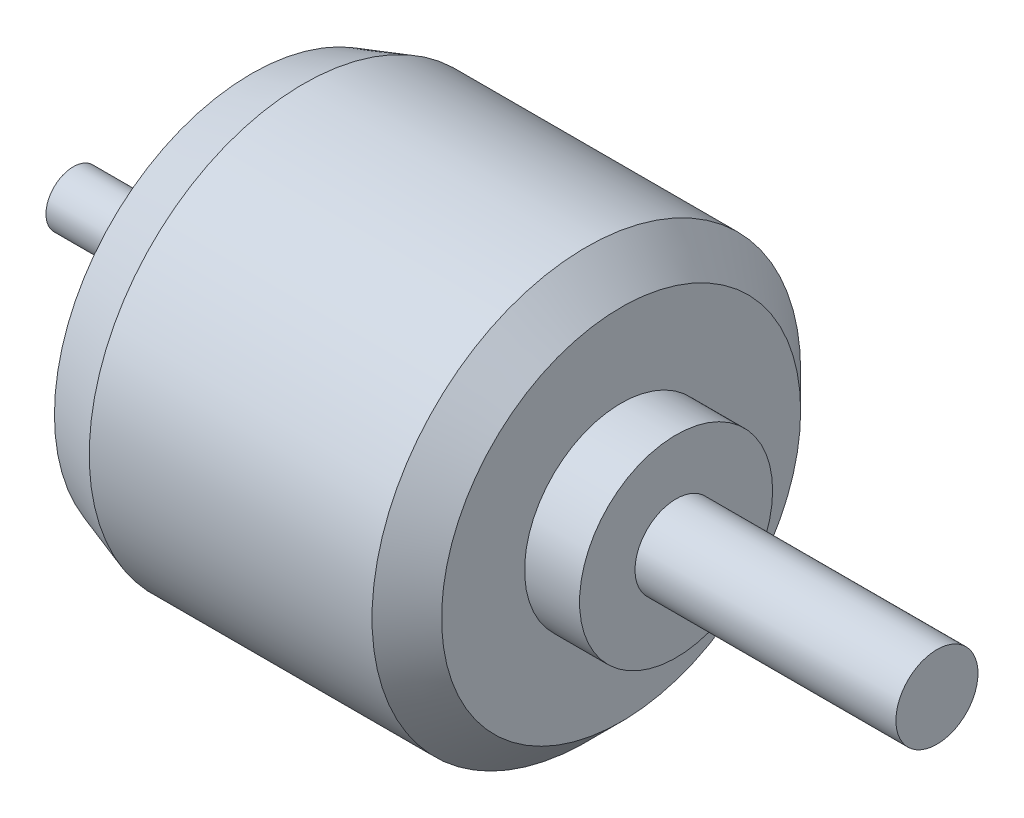
SolidWorks part; units mm, degrees
ref_plane "Front Plane" through (0, 0, 0) normal (0, 0, 1) x (1, 0, 0)
ref_plane "Top Plane" through (0, 0, 0) normal (0, 1, 0) x (1, 0, 0)
ref_plane "Right Plane" through (0, 0, 0) normal (1, 0, 0) x (0, 0, -1)
sketch "Sketch2" plane through (0, 0, 0) normal (1, 0, 0) x (0, 0, -1)
  circle A0 centre (0, 0) radius 4
  dimension "D1" = 8
extrude "Boss-Extrude1" add sketch "Sketch2" along normal blind 26
sketch "Sketch3" plane through (26, 0, 0) normal (1, 0, 0) x (0, 0, -1)
  circle A0 centre (0, 0) radius 31.3
  dimension "D1" = 62.6
extrude "Boss-Extrude2" add sketch "Sketch3" along normal blind 54
sketch "Sketch4" plane through (26, 0, 0) normal (-1, 0, 0) x (0, 0, 1)
  line L0 (0, 22) -> (0, -22)
  line L1 (-15, 0) -> (15, 0)
  circle A0 centre (0, 22) radius 2
  circle A1 centre (0, -22) radius 2
  circle A2 centre (-15, 0) radius 2
  circle A3 centre (15, 0) radius 2
  circle A4 centre (22, 0) radius 2
  circle A5 centre (0, -22) radius 2
  circle A6 centre (-22, 0) radius 2
  circle A7 centre (0, 15) radius 2
  circle A8 centre (15, 0) radius 2
  circle A9 centre (0, -15) radius 2
  point P5 (0, 0)
  point P9 (0, 0)
  point P22 (0, 0)
  point P29 (0, 0)
  dimension "D3" = 4
  dimension "D4" = 4
  dimension "D5" = 4
  dimension "D6" = 4
  dimension "D1" = 44
  dimension "D2" = 30
  dimension "D7" = 4
  dimension "D8" = 4
extrude "Cut-Extrude1" cut sketch "Sketch4" against normal blind 8
chamfer "Chamfer1" distance 2.54 distance2 7.62 1 edges at (26, 0, -31.3)
chamfer "Chamfer2" distance 5.08 1 edges at (80, 0, -31.3)
sketch "Sketch5" plane through (80, 0, 0) normal (1, 0, 0) x (0, 0, -1)
  circle A0 centre (0, 0) radius 14.097
  dimension "D1" = 28.194
extrude "Boss-Extrude3" add sketch "Sketch5" along normal blind 8.0264
sketch "Sketch6" plane through (88.0264, 0, 0) normal (1, 0, 0) x (0, 0, -1)
  circle A0 centre (0, 0) radius 5.9944
  dimension "D1" = 11.9888
extrude "Boss-Extrude4" add sketch "Sketch6" along normal blind 38.1
